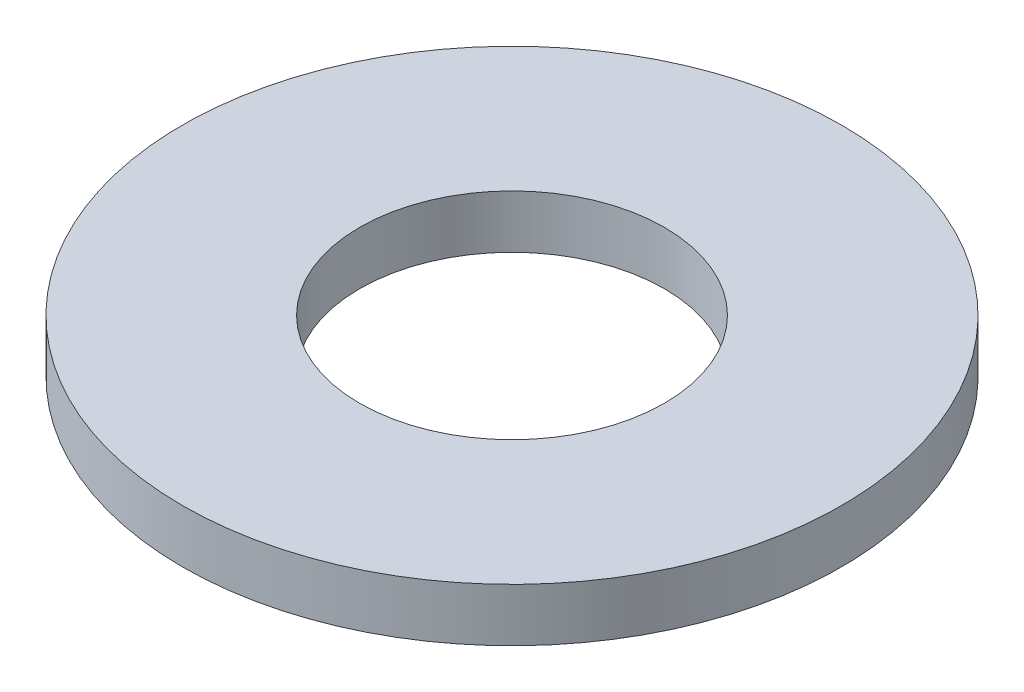
SolidWorks part; units mm, degrees
ref_plane "前视基准面" through (0, 0, 0) normal (0, 0, 1) x (1, 0, 0)
ref_plane "上视基准面" through (0, 0, 0) normal (0, 1, 0) x (1, 0, 0)
ref_plane "右视基准面" through (0, 0, 0) normal (1, 0, 0) x (0, 0, -1)
sketch "草图1" plane through (0, 0, 0) normal (0, 1, 0) x (1, 0, 0)
  circle A0 centre (0, 0) radius 4.3
  circle A1 centre (0, 0) radius 9.3
  dimension "D1" = 8.6
  dimension "D2" = 5
extrude "凸台-拉伸1" add sketch "草图1" along normal blind 1.5
